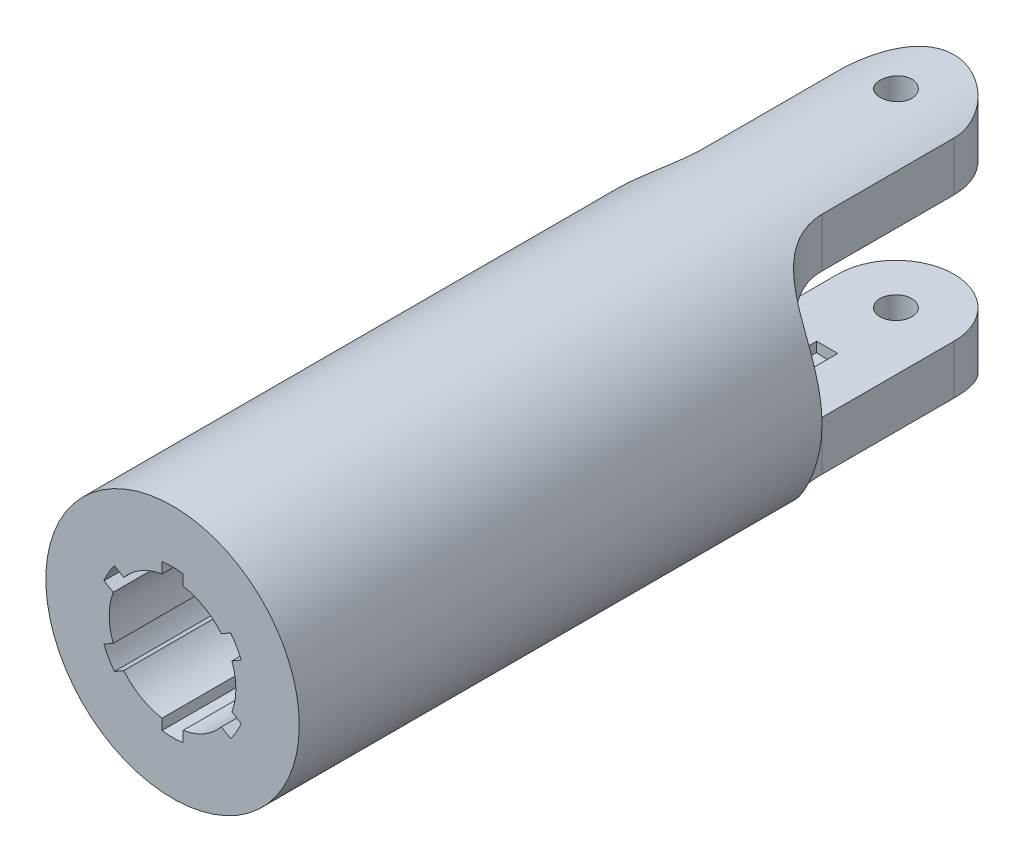
SolidWorks part; units mm, degrees
ref_plane "前视基准面" through (0, 0, 0) normal (0, 0, 1) x (1, 0, 0)
ref_plane "上视基准面" through (0, 0, 0) normal (0, 1, 0) x (1, 0, 0)
ref_plane "右视基准面" through (0, 0, 0) normal (1, 0, 0) x (0, 0, -1)
sketch "草图1" plane through (0, 0, 0) normal (0, 0, 1) x (1, 0, 0)
  circle A0 centre (0, 0) radius 6
  circle A1 centre (0, 0) radius 2.5
  dimension "D1" = 12
  dimension "D2" = 5
extrude "凸台-拉伸1" add sketch "草图1" along normal blind 37
sketch "草图2" plane through (0, 0, 0) normal (0, 1, 0) x (1, 0, 0)
  line L0 (0, 3.1848) -> (0, -21.7389) construction
  line L1 (-11.4446, -9) -> (14.3905, -9) construction
  line L2 (-2.75, -2.75) -> (-2.75, -9)
  line L4 (-6, 0) -> (-6, -37) construction
  line L5 (-6, -37) -> (6, -37) construction
  line L6 (-6, -2.0062) -> (-6, -15.979) construction
  line L7 (-6, -12.25) -> (-6, -37)
  line L8 (-6, -37) -> (6, -37)
  line L9 (6, -12.25) -> (6, -37)
  line L10 (2.75, -2.75) -> (2.75, -9)
  arc A0 (2.75, -2.75) -> (-2.75, -2.75) centre (0, -2.75) ccw
  arc A2 (-6, -12.25) -> (-2.75, -9) centre (-6, -9) ccw
  arc A3 (6, -12.25) -> (2.75, -9) centre (6, -9) cw
  circle A4 centre (0, -2.75) radius 0.75
  dimension "D1" = 5.5
  dimension "D2" = 28
  dimension "D3" = 1.5
extrude "切除-拉伸1" cut sketch "草图2" against normal mid plane 19 flip side to cut
sketch "草图3" plane through (0, 0, 0) normal (1, 0, 0) x (0, 0, -1)
  line L0 (-21.1395, 0) -> (4.4517, 0) construction
  line L6 (-9.25, 3) -> (0.9665, 3)
  line L7 (0.9665, 3) -> (0.9665, -3)
  line L8 (0.9665, -3) -> (-9.25, -3)
  arc A2 (-9.25, 3) -> (-9.25, -3) centre (-9.25, 0) ccw
  spline S2 degree 3 poles (-9, 5.3327) (-9.3489, 5.3327) (-9.6897, 5.3051) (-10.1779, 5.2159) (-10.3329, 5.1787) (-10.6283, 5.0872) (-10.7698, 5.0323) (-11.0313, 4.9047) (-11.1508, 4.8325) (-11.3691, 4.6696) (-11.4686, 4.5779) (-11.6436, 4.3792) (-11.7196, 4.2721) (-11.8523, 4.0422) (-11.9093, 3.9185) (-12.0526, 3.5326) (-12.1137, 3.2543) (-12.1762, 2.8069) (-12.192, 2.6524) (-12.2163, 2.34) (-12.2248, 2.1814) (-12.2435, 1.6983) (-12.2472, 1.3667) (-12.2504, 0.6843) (-12.25, 0.3412) (-12.25, -0.3433) (-12.2504, -0.687) (-12.2472, -1.3688) (-12.2435, -1.6999) (-12.2185, -2.3429) (-12.1972, -2.6566) (-12.1136, -3.2548) (-12.0524, -3.5333) (-11.9091, -3.9189) (-11.8521, -4.0427) (-11.7194, -4.2724) (-11.6436, -4.3792) (-11.4694, -4.577) (-11.3699, -4.6689) (-11.1511, -4.8323) (-11.032, -4.9042) (-10.7735, -5.0307) (-10.6328, -5.0857) (-10.3348, -5.1783) (-10.1798, -5.2154) (-9.8578, -5.2745) (-9.6895, -5.2965) (-9.3474, -5.3255) (-9.1746, -5.3327) (-9, -5.3327) knots 0 0 0 0 0.0625 0.0625 0.09375 0.09375 0.125 0.125 0.15625 0.15625 0.1875 0.1875 0.21875 0.21875 0.25 0.25 0.3125 0.3125 0.34375 0.34375 0.375 0.375 0.4375 0.4375 0.5 0.5 0.5625 0.5625 0.625 0.625 0.6875 0.6875 0.75 0.75 0.78125 0.78125 0.8125 0.8125 0.84375 0.84375 0.875 0.875 0.90625 0.90625 0.9375 0.9375 0.96875 0.96875 1 1 1 1 construction
  dimension "D1" = 6
extrude "切除-拉伸2" cut sketch "草图3" against normal mid plane 19
sketch "草图4" plane through (0, 0, 37) normal (0, 0, 1) x (1, 0, 0)
  line L0 (0, 7.1358) -> (0, -4.8157) construction
  line L1 (-0.5, 3.4641) -> (-0.5, 2.958)
  line L2 (0.5, 3.4641) -> (0.5, 2.958)
  line L3 (2.75, 2.1651) -> (2.3117, 1.912)
  line L4 (3.25, 1.299) -> (2.8117, 1.046)
  line L5 (3.25, -1.299) -> (2.8117, -1.046)
  line L6 (2.75, -2.1651) -> (2.3117, -1.912)
  line L7 (0.5, -3.4641) -> (0.5, -2.958)
  line L8 (-0.5, -3.4641) -> (-0.5, -2.958)
  line L9 (-2.75, -2.1651) -> (-2.3117, -1.912)
  line L10 (-3.25, -1.299) -> (-2.8117, -1.046)
  line L11 (-3.25, 1.299) -> (-2.8117, 1.046)
  line L12 (-2.75, 2.1651) -> (-2.3117, 1.912)
  line L13 (0, 0) -> (0.5, 2.958) construction
  arc A0 (-2.75, 2.1651) -> (-3.25, 1.299) centre (0, 0) ccw
  arc A1 (-0.5, 2.958) -> (-2.3117, 1.912) centre (0, 0) ccw
  arc A2 (0.5, 3.4641) -> (-0.5, 3.4641) centre (0, 0) ccw
  arc A3 (-2.8117, 1.046) -> (-2.8117, -1.046) centre (0, 0) ccw
  arc A4 (-2.3117, -1.912) -> (-0.5, -2.958) centre (0, 0) ccw
  arc A5 (0.5, -2.958) -> (2.3117, -1.912) centre (0, 0) ccw
  arc A6 (2.8117, -1.046) -> (2.8117, 1.046) centre (0, 0) ccw
  arc A7 (2.3117, 1.912) -> (0.5, 2.958) centre (0, 0) ccw
  arc A8 (-3.25, -1.299) -> (-2.75, -2.1651) centre (0, 0) ccw
  arc A9 (-0.5, -3.4641) -> (0.5, -3.4641) centre (0, 0) ccw
  arc A10 (2.75, -2.1651) -> (3.25, -1.299) centre (0, 0) ccw
  arc A11 (3.25, 1.299) -> (2.75, 2.1651) centre (0, 0) ccw
  dimension "D1" = 7
  dimension "D2" = 6
  dimension "D3" = 1
extrude "切除-拉伸3" cut sketch "草图4" against normal blind 31
